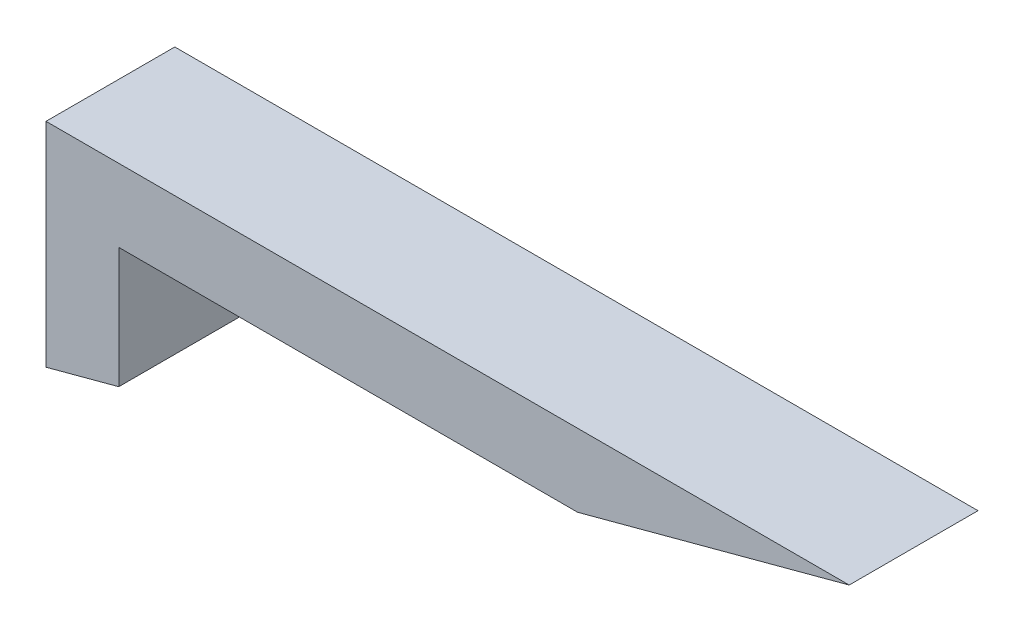
SolidWorks part; units mm, degrees
ref_plane "Front Plane" through (0, 0, 0) normal (0, 0, 1) x (1, 0, 0)
ref_plane "Top Plane" through (0, 0, 0) normal (0, 1, 0) x (1, 0, 0)
ref_plane "Right Plane" through (0, 0, 0) normal (1, 0, 0) x (0, 0, -1)
sketch "Sketch1" plane through (0, 0, 0) normal (0, 0, 1) x (1, 0, 0)
  line L0 (12.7, 6.8059) -> (-12.7, 0)
  line L1 (-12.7, 0) -> (12.7, 0)
  line L2 (-12.7, 0) -> (-12.7, 74.3309)
  line L3 (-12.7, 74.3309) -> (12.7, 74.3309)
  line L4 (12.7, 0) -> (12.7, 74.3309)
  line L5 (-12.7, 74.3309) -> (267.6507, 74.3309)
  line L6 (-12.7, 74.3309) -> (-12.7, 48.9309)
  line L7 (-12.7, 48.9309) -> (267.6507, 48.9309)
  line L8 (267.6507, 74.3309) -> (267.6507, 48.9309)
  line L9 (267.6507, 74.3309) -> (172.8566, 48.9309)
  point P4 (0, 0)
  point P10 (202.8718, 53.8391)
  point P12 (271.64, 77.2633)
  point P13 (-6.35, 73.2849)
  point P14 (274.0007, 74.3309)
  dimension "D1" = 15
  dimension "D2" = 15
  dimension "D3" = 25.4
extrude "Boss-Extrude1" add sketch "Sketch1" along normal blind 44.958 contours L7 L2 L0 L4 | L2 L7 L4 L3 | L9 L5 L4 L7
